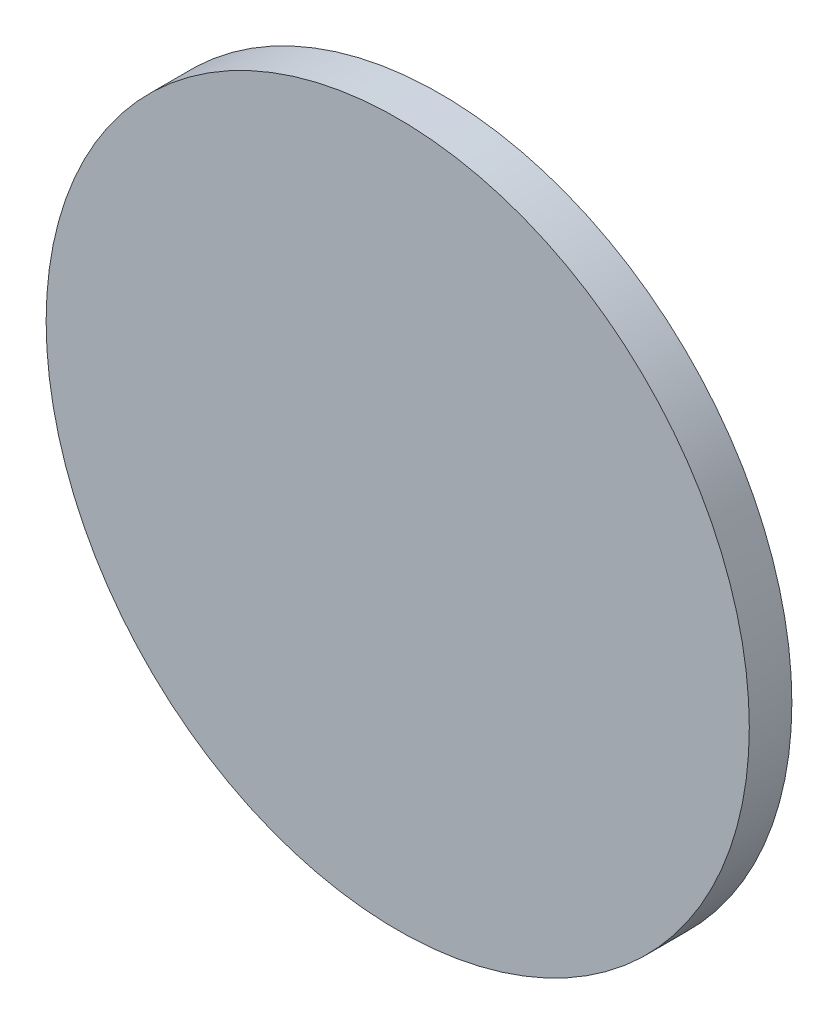
SolidWorks part; units mm, degrees
ref_plane "前视基准面" through (0, 0, 0) normal (0, 0, 1) x (1, 0, 0)
ref_plane "上视基准面" through (0, 0, 0) normal (0, 1, 0) x (1, 0, 0)
ref_plane "右视基准面" through (0, 0, 0) normal (1, 0, 0) x (0, 0, -1)
sketch "草图1" plane through (0, 0, 0) normal (0, 0, 1) x (1, 0, 0)
  circle A0 centre (108.615, 61.5656) radius 19
  dimension "D1" = 38
extrude "凸台-拉伸1" add sketch "草图1" along normal blind 2.3
